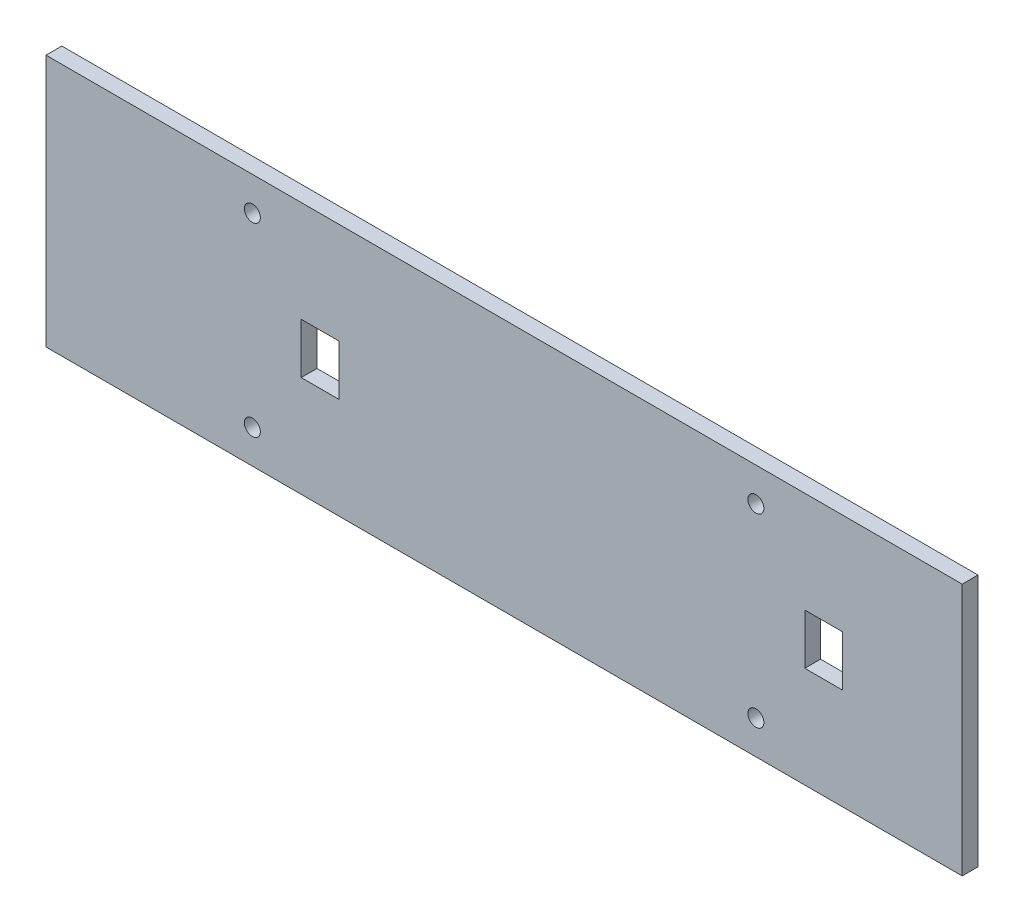
SolidWorks part; units mm, degrees
ref_plane "Front Plane" through (0, 0, 0) normal (0, 0, 1) x (1, 0, 0)
ref_plane "Top Plane" through (0, 0, 0) normal (0, 1, 0) x (1, 0, 0)
ref_plane "Right Plane" through (0, 0, 0) normal (1, 0, 0) x (0, 0, -1)
sketch "Sketch2" plane through (0, 0, 0) normal (0, 0, 1) x (1, 0, 0)
  line L1 (-92.075, -25.4) -> (92.075, -25.4)
  line L2 (-92.075, -25.4) -> (-92.075, 25.4)
  line L3 (-92.075, 25.4) -> (92.075, 25.4)
  line L4 (92.075, -25.4) -> (92.075, 25.4)
  line L5 (-92.075, -25.4) -> (92.075, 25.4) construction
  line L6 (-92.075, 25.4) -> (92.075, -25.4) construction
  point P0 (0, 0)
  dimension "D1" = 184.15
  dimension "D2" = 50.8
extrude "Boss-Extrude1" add sketch "Sketch2" along normal mid plane 3.175
sketch "Sketch3" plane through (0, 0, 1.5875) normal (0, 0, 1) x (1, 0, 0)
  line L0 (-40.78, 5.075) -> (-40.78, -5.075)
  line L1 (-40.78, 5.075) -> (-33.16, 5.075)
  line L2 (-40.78, -5.075) -> (-33.16, -5.075)
  line L3 (-33.16, 5.075) -> (-33.16, -5.075)
  line L4 (60.43, 5.075) -> (60.43, -5.075)
  line L5 (60.43, 5.075) -> (68.05, 5.075)
  line L6 (60.43, -5.075) -> (68.05, -5.075)
  line L7 (68.05, 5.075) -> (68.05, -5.075)
  circle A0 centre (-50.605, 18.64) radius 1.61
  circle A1 centre (-50.605, -18.64) radius 1.61
  circle A2 centre (50.605, 18.64) radius 1.61
  circle A3 centre (50.605, -18.64) radius 1.61
  dimension "D1" = 3.22
  dimension "D2" = 7.62
  dimension "D3" = 7.62
extrude "Cut-Extrude1" cut sketch "Sketch3" against normal blind 5.08
